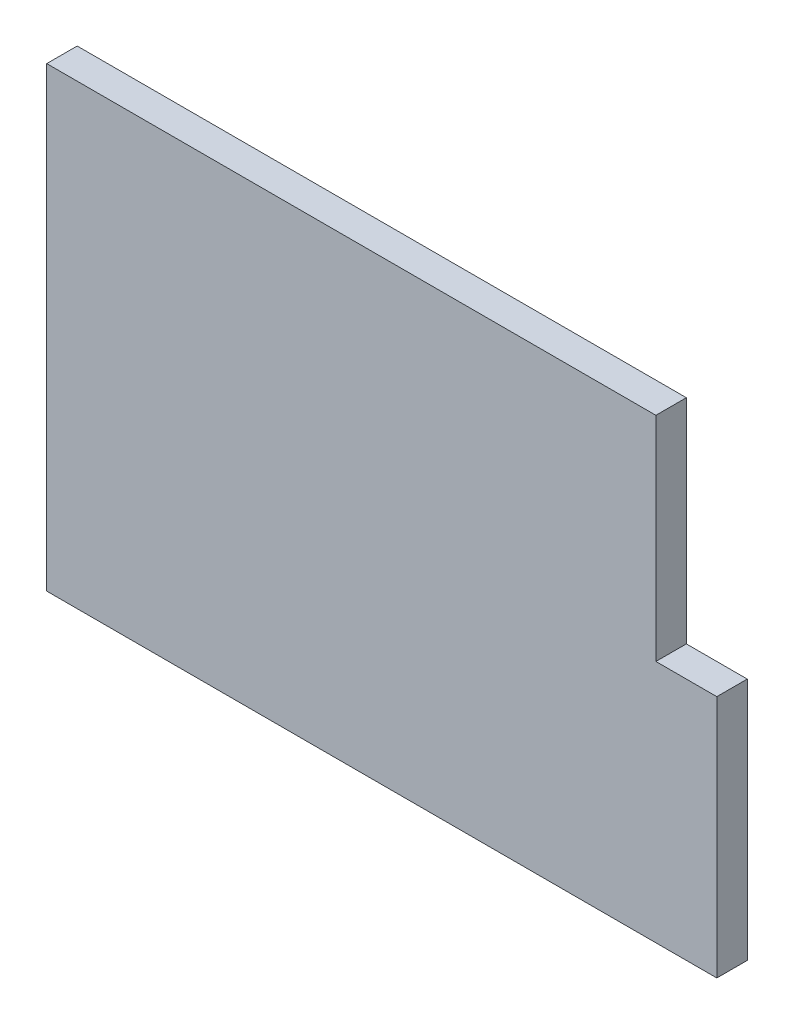
SolidWorks part; units mm, degrees
ref_plane "Front Plane" through (0, 0, 0) normal (0, 0, 1) x (1, 0, 0)
ref_plane "Top Plane" through (0, 0, 0) normal (0, 1, 0) x (1, 0, 0)
ref_plane "Right Plane" through (0, 0, 0) normal (1, 0, 0) x (0, 0, -1)
sketch "Sketch1" plane through (0, 0, 0) normal (0, 0, 1) x (1, 0, 0)
  line L1 (-10, -7.5) -> (10, -7.5)
  line L2 (-10, -7.5) -> (-10, 7.5)
  line L3 (-10, 7.5) -> (10, 7.5)
  line L4 (10, 0.5) -> (10, 7.5)
  line L5 (-10, -7.5) -> (10, 7.5) construction
  line L6 (-10, 7.5) -> (10, -7.5) construction
  line L11 (10, -7.5) -> (12, -7.5)
  line L13 (10, 0.5) -> (12, 0.5)
  line L14 (12, -7.5) -> (12, 0.5)
  point P0 (0, 0)
  dimension "D1" = 20
  dimension "D2" = 15
  dimension "D3" = 2
  dimension "D4" = 8
extrude "Boss-Extrude1" add sketch "Sketch1" along normal blind 1
